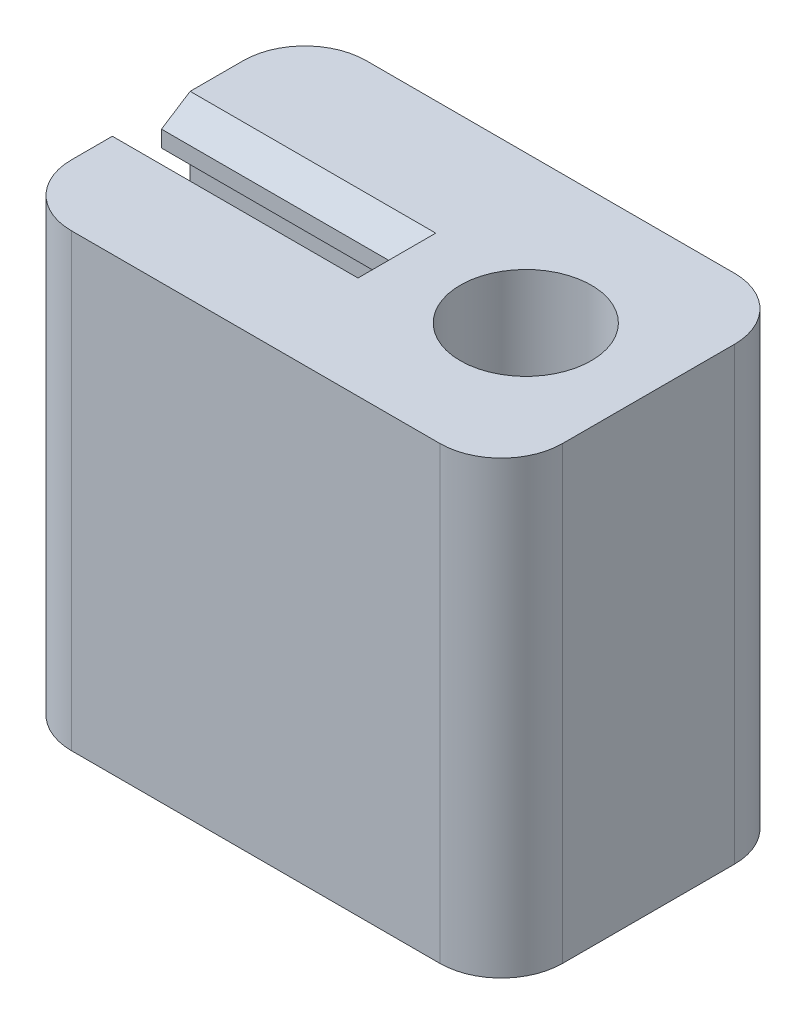
SolidWorks part; units mm, degrees
material "ABS"
ref_plane "Front Plane" through (0, 0, 0) normal (0, 0, 1) x (1, 0, 0)
ref_plane "Top Plane" through (0, 0, 0) normal (0, 1, 0) x (1, 0, 0)
ref_plane "Right Plane" through (0, 0, 0) normal (1, 0, 0) x (0, 0, -1)
sketch "Sketch1" plane through (0, 0, 0) normal (0, 1, 0) x (1, 0, 0)
  line L0 (-6, 0) -> (6, 0) construction
  line L1 (-4.5, -3.6) -> (4.5, -3.6)
  line L2 (-6, -2.1) -> (-6, 2.1)
  line L3 (-4.5, 3.6) -> (4.5, 3.6)
  line L4 (6, -2.1) -> (6, 2.1)
  line L5 (-6, -3.6) -> (6, 3.6) construction
  line L6 (-6, 3.6) -> (6, -3.6) construction
  circle A0 centre (3, 0) radius 1.6
  arc A1 (4.5, 3.6) -> (6, 2.1) centre (4.5, 2.1) cw
  arc A2 (6, -2.1) -> (4.5, -3.6) centre (4.5, -2.1) cw
  arc A3 (-4.5, -3.6) -> (-6, -2.1) centre (-4.5, -2.1) cw
  arc A4 (-6, 2.1) -> (-4.5, 3.6) centre (-4.5, 2.1) cw
  point P0 (0, 0)
  dimension "D3" = 3.2
  dimension "D4" = 3
  dimension "D5" = 1.5
  dimension "D1" = 7.2
  dimension "D2" = 12
extrude "Boss-Extrude1" add sketch "Sketch1" against normal blind 11
sketch "Sketch2" plane through (-6, 0, 0) normal (-1, 0, 0) x (0, 0, 1)
  line L0 (-3.6, -11) -> (-3.6, 0) construction
  line L1 (-2.1, 0) -> (2.1, 0) construction
  line L2 (-2.1, -11) -> (2.1, -11) construction
  line L3 (0, 0) -> (0, -11) construction
  line L4 (1.1, -11) -> (-0.3334, -11)
  line L5 (1.1, 0) -> (1.1, -11)
  line L6 (1.1, 0) -> (-0.8, 0)
  line L7 (-0.8, 0) -> (-0.1, -0.45)
  line L8 (-0.1, -0.45) -> (-0.1, -0.85)
  line L9 (-0.1, -0.85) -> (-0.8, -1.3)
  line L10 (-0.8, -1.3) -> (-0.8, -1.65)
  line L11 (-0.1, -0.65) -> (-0.8, -0.65) construction
  line L12 (-0.8, 0) -> (-0.8, 0.35)
  line L13 (-0.8, 0) -> (-0.8, -1.3) construction
  line L14 (-0.8, -2) -> (-0.8, -1.65)
  line L15 (-0.8, -2) -> (-0.1, -2.45)
  line L16 (-0.1, -2.45) -> (-0.1, -2.85)
  line L17 (-0.1, -2.85) -> (-0.8, -3.3)
  line L18 (-0.8, -3.3) -> (-0.8, -3.65)
  line L19 (-0.8, -4) -> (-0.8, -3.65)
  line L20 (-0.8, -4) -> (-0.1, -4.45)
  line L21 (-0.1, -4.45) -> (-0.1, -4.85)
  line L22 (-0.1, -4.85) -> (-0.8, -5.3)
  line L23 (-0.8, -5.3) -> (-0.8, -5.65)
  line L24 (-0.8, -6) -> (-0.8, -5.65)
  line L25 (-0.8, -6) -> (-0.1, -6.45)
  line L26 (-0.1, -6.45) -> (-0.1, -6.85)
  line L27 (-0.1, -6.85) -> (-0.8, -7.3)
  line L28 (-0.8, -7.3) -> (-0.8, -7.65)
  line L29 (-0.8, -8) -> (-0.8, -7.65)
  line L30 (-0.8, -8) -> (-0.1, -8.45)
  line L31 (-0.1, -8.45) -> (-0.1, -8.85)
  line L32 (-0.1, -8.85) -> (-0.8, -9.3)
  line L33 (-0.8, -9.3) -> (-0.8, -9.65)
  line L34 (-0.8, -10) -> (-0.8, -9.65)
  line L35 (-0.8, -10) -> (-0.1, -10.45)
  line L36 (-0.1, -10.45) -> (-0.1, -10.85)
  line L37 (-0.1, -10.85) -> (-0.3334, -11)
  line L40 (-0.8, -11.3) -> (-0.8, -11.65) [skipped]
  point P9 (-0.8, -0.65)
  line M1 (2.1, 0) -> (-2.1, 0)
  line M3 (-2.1, -11) -> (2.1, -11)
  dimension "D1" = 1.2
  dimension "D2" = 0.7
  dimension "D3" = 6
  dimension "D4" = 0.35
  dimension "D5" = 0.4
  dimension "D6" = 3.5
  dimension "D7" = 2
  dimension "D9" = 0.35
  dimension "D10" = 2
extrude "Cut-Extrude1" cut sketch "Sketch2" against normal blind 6 contours L36 L37 L5 L7 L8 L9 L10 L14 L15 L16 L17 L18 L19 L20 L21 L22 L23 L24 L25 L26 L27 L28 L29 L30 L31 L32 L33 L34 L35 M3 M1
sketch "Sketch3" [suppressed] plane through (0, -11, 0) normal (0, -1, 0) x (1, 0, 0)
  line L12 (0, 1.1) -> (-6, 1.1) construction
  line L13 (0, -0.3334) -> (0, 1.1) construction
  line L14 (0, -0.3334) -> (-6, -0.3334) construction
  line L15 (-4.5, -6.6) -> (4.5, -6.6)
  line L16 (9, -2.1) -> (9, 2.1)
  line L17 (4.5, 6.6) -> (-4.5, 6.6)
  line L18 (-4.5, -6.6) -> (4.5, -6.6)
  line L19 (9, -2.1) -> (9, 2.1)
  line L20 (4.5, 6.6) -> (-4.5, 6.6)
  line L21 (0, 1.1) -> (-9, 1.1)
  line L22 (0, -0.3334) -> (0, 1.1)
  line L23 (0, -0.3334) -> (-9, -0.3334)
  line L24 (-9, 2.1) -> (-9, 1.1)
  line L25 (-9, -0.3334) -> (-9, -2.1)
  arc A20 (-9, -2.1) -> (-4.5, -6.6) centre (-4.5, -2.1) ccw
  arc A21 (4.5, -6.6) -> (9, -2.1) centre (4.5, -2.1) ccw
  arc A22 (9, 2.1) -> (4.5, 6.6) centre (4.5, 2.1) ccw
  arc A23 (-4.5, 6.6) -> (-9, 2.1) centre (-4.5, 2.1) ccw
  arc A24 (-9, -2.1) -> (-4.5, -6.6) centre (-4.5, -2.1) ccw
  arc A25 (4.5, -6.6) -> (9, -2.1) centre (4.5, -2.1) ccw
  arc A26 (9, 2.1) -> (4.5, 6.6) centre (4.5, 2.1) ccw
  arc A27 (-4.5, 6.6) -> (-9, 2.1) centre (-4.5, 2.1) ccw
  dimension "D1" = 3
extrude "Boss-Extrude2" [suppressed] add sketch "Sketch3" against normal blind 0.44
